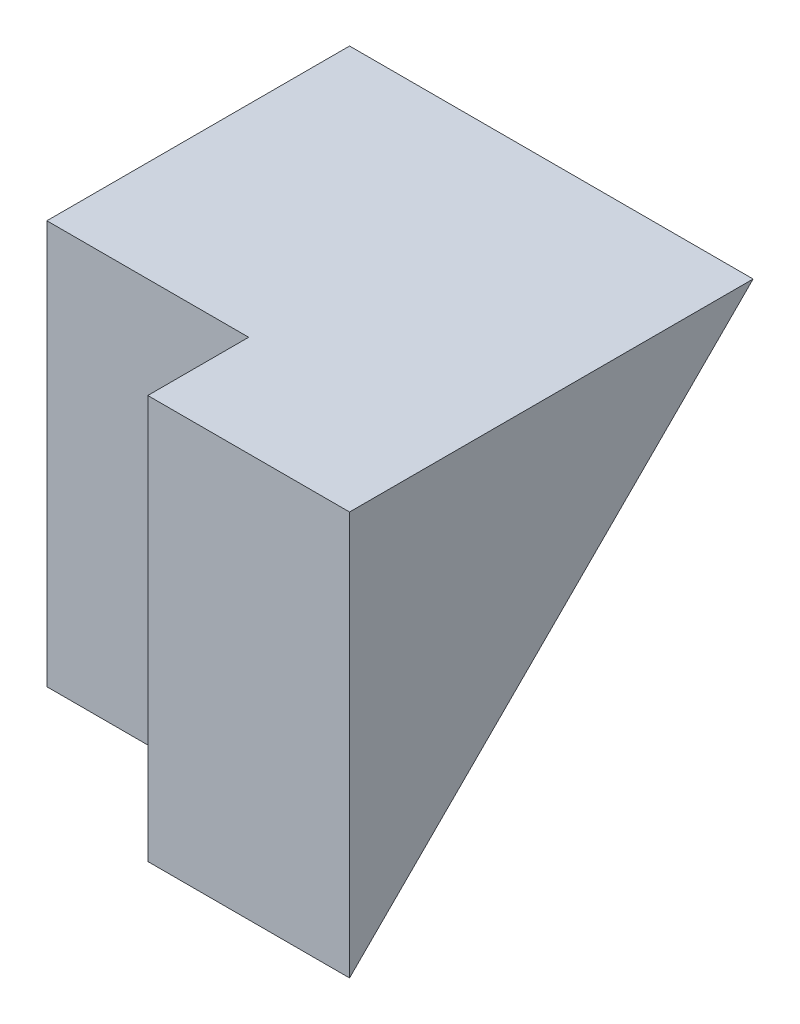
SolidWorks part; units mm, degrees
ref_plane "Front Plane" through (0, 0, 0) normal (0, 0, 1) x (1, 0, 0)
ref_plane "Top Plane" through (0, 0, 0) normal (0, 1, 0) x (1, 0, 0)
ref_plane "Right Plane" through (0, 0, 0) normal (1, 0, 0) x (0, 0, -1)
sketch "Sketch1" plane through (0, 0, 0) normal (1, 0, 0) x (0, 0, -1)
  line L1 (0, 0) -> (4, 0)
  line L2 (0, 0) -> (0, 4)
  line L3 (0, 4) -> (4, 4)
  line L4 (4, 0) -> (4, 4)
  dimension "D1" = 4
  dimension "D2" = 4
extrude "Boss-Extrude1" add sketch "Sketch1" along normal blind 2
sketch "Sketch2" plane through (0, 0, 0) normal (-1, 0, 0) x (0, 0, 1)
  line L0 (-1, 0) -> (-1, 4)
  line L1 (0, 0) -> (-4, 0) construction
  line L2 (-4, 0) -> (-4, 4) construction
  line L3 (-4, 4) -> (-4, 0)
  line L4 (-4, 0) -> (-1, 0)
  line L5 (-4, 4) -> (0, 4) construction
  line L6 (-1, 4) -> (-4, 4)
  dimension "D1" = 3
  dimension "D2" = 4
extrude "Boss-Extrude2" add sketch "Sketch2" along normal blind 2
sketch "Sketch3" plane through (2, 0, 0) normal (1, 0, 0) x (0, 0, -1)
  line L0 (0, 0) -> (4, 4)
  line L1 (4, 4) -> (0, 4)
  line L2 (0, 4) -> (0, 0)
  line M5 (0, 0) -> (4, 0)
  line M6 (4, 0) -> (4, 4)
extrude "Cut-Extrude1" cut sketch "Sketch3" against normal blind 2 contours L0 M5 M6
